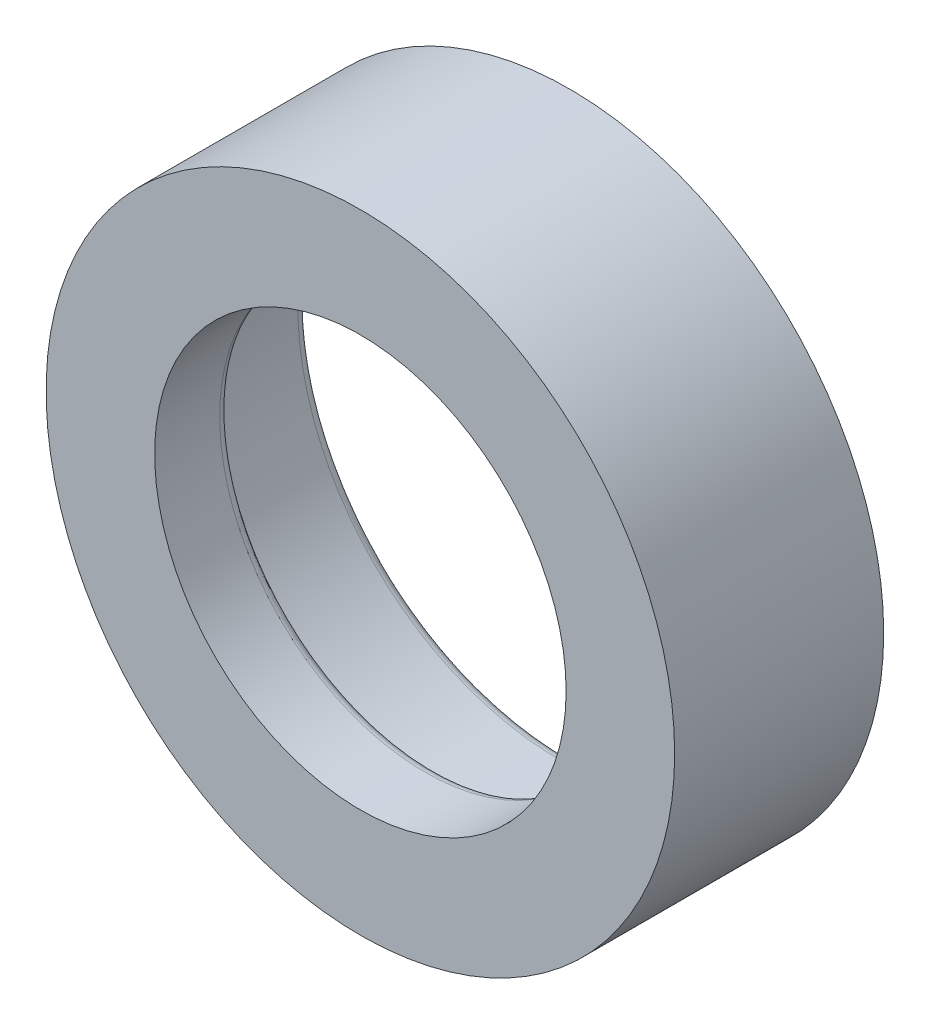
SolidWorks part; units mm, degrees
ref_plane "Front Plane" through (0, 0, 0) normal (0, 0, 1) x (1, 0, 0)
ref_plane "Top Plane" through (0, 0, 0) normal (0, 1, 0) x (1, 0, 0)
ref_plane "Right Plane" through (0, 0, 0) normal (1, 0, 0) x (0, 0, -1)
sketch "Sketch1" plane through (0, 0, 0) normal (0, 0, 1) x (1, 0, 0)
  circle A0 centre (0, 0) radius 30.55
extrude "Boss-Extrude1" add sketch "Sketch1" along normal blind 20.32
sketch "Sketch2" plane through (0, 0, 0) normal (0, 0, -1) x (1, 0, 0)
  circle A0 centre (0, 0) radius 25.404
extrude "Cut-Extrude1" cut sketch "Sketch2" against normal blind 13
sketch "Sketch3" plane through (0, 0, 20.32) normal (0, 0, 1) x (1, 0, 0)
  circle A0 centre (0, 0) radius 20
extrude "Cut-Extrude2" cut sketch "Sketch3" against normal through all
fillet "Fillet1" radius 1 1 edges at (0, 25.404, 0)
fillet "Fillet2" radius 1 1 edges at (0, 20, 13)
